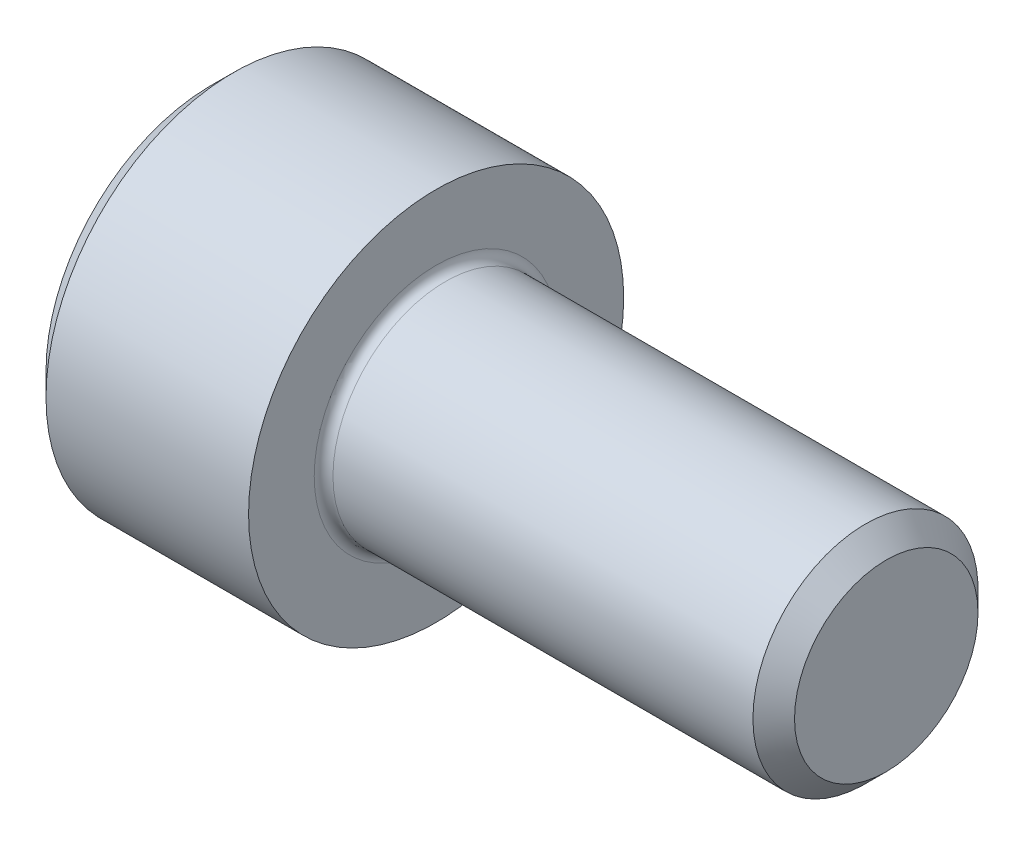
SolidWorks part; units mm, degrees
revolve "Base-Revolve" add sketch "BodySke"
sketch "BodySke" plane through (0, 0, 0) normal (0, 0, 1) x (1, 0, 0)
  line L0 (0, 0) -> (0, 4.4)
  line L1 (0.6, 5) -> (6, 5)
  line L2 (6, 5) -> (6, 3)
  line L3 (6, 3) -> (17.4455, 3)
  line L4 (18, 2.4455) -> (18, 0)
  line L5 (18, 0) -> (0, 0)
  line L6 (-31.75, 0) -> (127, 0) construction
  line L7 (0, 4.4) -> (0.6, 5)
  line L8 (18, 2.4455) -> (17.4455, 3)
  line L9 (0, -4.4) -> (0.6, -5) construction
  line L10 (18, -2.4455) -> (17.4455, -3) construction
  line L11 (7, 9.525) -> (7, 3.175) construction
  line L12 (6, 9.525) -> (6, 3.175) construction
  line L13 (-32, 9.525) -> (-32, 3.175) construction
  dimension "Diameter" = 6
  dimension "Head_ht" = 6
  dimension "Length" = 12
  dimension "Body_ch_ang" = 45
  dimension "Head_dia" = 10
  dimension "Head_ch_ang" = 45
  dimension "Minor_dia" = 4.891
  dimension "Advance" = 1
  dimension "Thread_nom" = 12
  dimension "Thread_length" = 50
  dimension "Head_ch_ht" = 0.6
cosmetic thread "ThreadCosmetic"
fillet "Fillet1" radius 0.25 1 edges at (6, 0, 3)
ref_plane "Plane1" through (0, 0, 0) normal (0, 0, 1) x (1, 0, 0)
ref_plane "Plane2" through (0, 0, 0) normal (0, 1, 0) x (1, 0, 0)
ref_plane "Plane3" through (0, 0, 0) normal (1, 0, 0) x (0, 0, -1)
sketch "Sketch2" plane through (0, 0, 0) normal (0, 0, 1) x (1, 0, 0)
  line L0 (0, 2.542) -> (3, 2.542)
  line L1 (3, 2.542) -> (4.4676, 0)
  line L2 (-31.75, 0) -> (127, 0) construction
  line L3 (4.4676, 0) -> (0, 0)
  line L4 (0, 0) -> (0, 2.542)
  line L5 (0, 4.4) -> (0, -4.4) construction
  line L6 (0, 0) -> (47.625, 0) construction
  line L7 (6, -5) -> (6, 5) construction
  dimension "D1" = 2.542
  dimension "D2" = 60
revolve "Hex-PreBroach" cut sketch "Sketch2" angle 360 about L6
sketch "Sketch3" plane through (0, 0, 0) normal (-1, 0, 0) x (0, 0.5, 0.866)
  line L0 (1.4676, 2.542) -> (-1.4676, 2.542)
  line L1 (-1.4676, 2.542) -> (-2.9352, 0)
  line L2 (1.4676, 2.542) -> (2.9352, 0)
  line L3 (1.4676, -2.542) -> (2.9352, 0)
  line L4 (1.4676, -2.542) -> (-1.4676, -2.542)
  line L5 (-1.4676, -2.542) -> (-2.9352, 0)
  dimension "D1" = 2.542
  dimension "D2" = 2.542
  dimension "Hex_size" = 5.084
extrude "Hex" cut sketch "Sketch3" against normal blind 3
sketch "Sketch4" plane through (0, 0, 0) normal (-1, 0, 0) x (0, 0, 1)
  line L0 (0, 0) -> (2.8067, 0)
  line L1 (0, 0) -> (6.1484, 3.5498) construction
  line L2 (0, 0) -> (1.4033, 2.4307)
  line L3 (2.3336, 0.614) -> (2.6851, 0.817)
  line L4 (1.6986, 1.7139) -> (2.0501, 1.9169)
  arc A0 (2.3336, 0.614) -> (1.6986, 1.7139) centre (0, 0) ccw
  arc A1 (2.8067, 0) -> (2.6851, 0.817) centre (0, 0) ccw
  arc A2 (1.4033, 2.4307) -> (2.0501, 1.9169) centre (0, 0) cw
  dimension "D1" = 30
  dimension "D2" = 60
  dimension "Spline_p_dim" = 1.27
  dimension "D3" = 0.635
extrude "Spline" [suppressed] cut sketch "Sketch4" against normal blind 3
pattern_circular "CirPattern1" [suppressed] count 6 every 60
sketch "Sketch5" plane through (0, 0, 0) normal (0, 0, 1) x (1, 0, 0)
  line L0 (-31.75, 0) -> (127, 0) construction
  line L2 (0, 4.4) -> (0, -4.4) construction
  circle A0 centre (2.3, 0) radius 0.675
  dimension "Drilled_hole_dia" = 1.35
  dimension "Drilled_hole_loc" = 2.3
extrude "Hole" [suppressed] cut sketch "Sketch5" against normal through all and the other way through all
pattern_circular "Drilled-4" [suppressed] count 2 every 60
pattern_circular "Drilled-6" [suppressed] count 3 every 60
sketch "ThdSchSke" plane through (0, 0, 0) normal (0, 0, 1) x (1, 0, 0)
  line L0 (7, -2.4455) -> (6.6117, -3)
  line L1 (7, -2.4455) -> (7.3883, -3)
  line L2 (7.3883, -3) -> (7.3883, -3.75)
  line L3 (-3.175, 0) -> (5.1513, 0) construction
  line L5 (7.3883, -3.75) -> (6.6117, -3.75)
  line L6 (6.6117, -3.75) -> (6.6117, -3)
  line L7 (0, 4.4) -> (0, -4.4) construction
  dimension "Thread_minor" = 4.891
  dimension "Diameter" = 6
  dimension "Start" = 7
revolve "ThreadSchematic" [suppressed] cut sketch "ThdSchSke" angle 360 about L3
pattern_linear "ThdSchPat" [suppressed]
equation "\"D2@Sketch3\" = \"Hex_size@Sketch3\" / 2"
equation "\"D1@Sketch3\" = \"Hex_size@Sketch3\" / 2"
equation "\"D1@Sketch2\" = \"Hex_size@Sketch3\" / 2"
equation "\"D3@Sketch4\" = \"Spline_p_dim@Sketch4\" / 2"
equation "\"Thread_minor@ThreadCosmetic\"  =  \"Minor_dia@BodySke\""
equation "\"D2@CirPattern1\" = 360 / \"Num_teeth@CirPattern1\""
equation "\"Wall_thickness@Sketch2\" = \"Head_ht@BodySke\" - \"Key_eng@Hex\""
equation "\"Thread_length@ThreadCosmetic\" = ((sgn( (\"Length@BodySke\" - \"Advance@BodySke\" ) - \"Thread_nom@BodySke\" )-1)*( (\"Length@BodySke\" - \"Advance@BodySke\" ) - \"Thread_nom@BodySke\" ))/-2+ \"Thread_nom@BodySke\""
equation "\"Thread_minor@ThdSchSke\" = \"Minor_dia@BodySke\""
equation "\"Diameter@ThdSchSke\" = \"Diameter@BodySke\""
equation "\"Overcut@ThdSchSke\" = \"Diameter@BodySke\" * 1.25"
equation "\"Start@ThdSchSke\" = \"Head_ht@BodySke\" + \"Length@BodySke\" - \"Thread_length@ThreadCosmetic\"  '---Non-countersunk---"
equation "\"Num_threads@ThdSchPat\" = int( \"Thread_length@ThreadCosmetic\" / \"Advance@BodySke\" + 0.999 )  + 1"
equation "\"Advance@ThdSchPat\" = \"Thread_length@ThreadCosmetic\" /  (\"Num_threads@ThdSchPat\" - 1) 'relax it"
equation "\"Num_threads@ThdSchPat\" = \"Num_threads@ThdSchPat\" - sgn( \"Num_threads@ThdSchPat\" - 1) '---chamfered tips only---"
